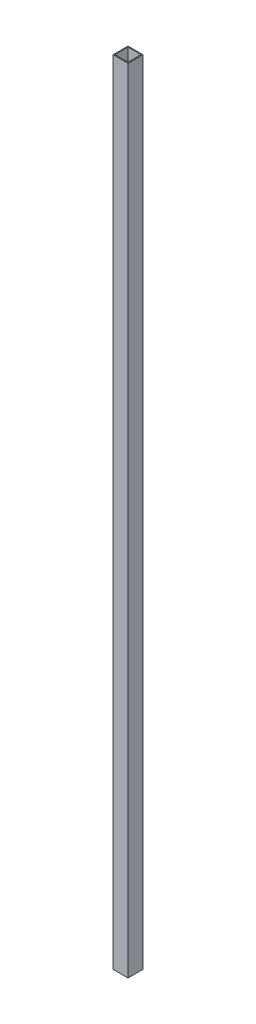
SolidWorks part; units mm, degrees
ref_plane "Front Plane" through (0, 0, 0) normal (0, 0, 1) x (1, 0, 0)
ref_plane "Top Plane" through (0, 0, 0) normal (0, 1, 0) x (1, 0, 0)
ref_plane "Right Plane" through (0, 0, 0) normal (1, 0, 0) x (0, 0, -1)
sketch "Sketch2" plane through (0, 0, 0) normal (0, 1, 0) x (1, 0, 0)
  line L1 (-15, 15) -> (15, 15)
  line L2 (-15, 15) -> (-15, -15)
  line L3 (-15, -15) -> (15, -15)
  line L4 (15, 15) -> (15, -15)
  line L5 (-15, 15) -> (15, -15) construction
  line L6 (-15, -15) -> (15, 15) construction
  line L10 (-13, 13) -> (-13, -13)
  line L11 (-13, -13) -> (13, -13)
  line L12 (13, 13) -> (13, -13)
  line L13 (-13, 13) -> (13, 13)
  point P0 (0, 0)
  dimension "D1" = 30
  dimension "D2" = 30
  dimension "D3" = 2
extrude "Boss-Extrude1" add sketch "Sketch2" along normal mid plane 1586.03
